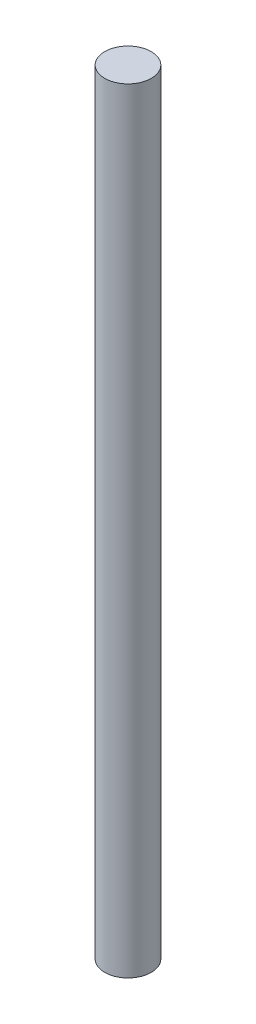
SolidWorks part; units mm, degrees
ref_plane "Front Plane" through (0, 0, 0) normal (0, 0, 1) x (1, 0, 0)
ref_plane "Top Plane" through (0, 0, 0) normal (0, 1, 0) x (1, 0, 0)
ref_plane "Right Plane" through (0, 0, 0) normal (1, 0, 0) x (0, 0, -1)
sketch "Sketch1" plane through (0, 0, 0) normal (0, 1, 0) x (1, 0, 0)
  circle A0 centre (0, 0) radius 0.3
  dimension "D1" = 0.6
extrude "Boss-Extrude1" add sketch "Sketch1" along normal blind 10
